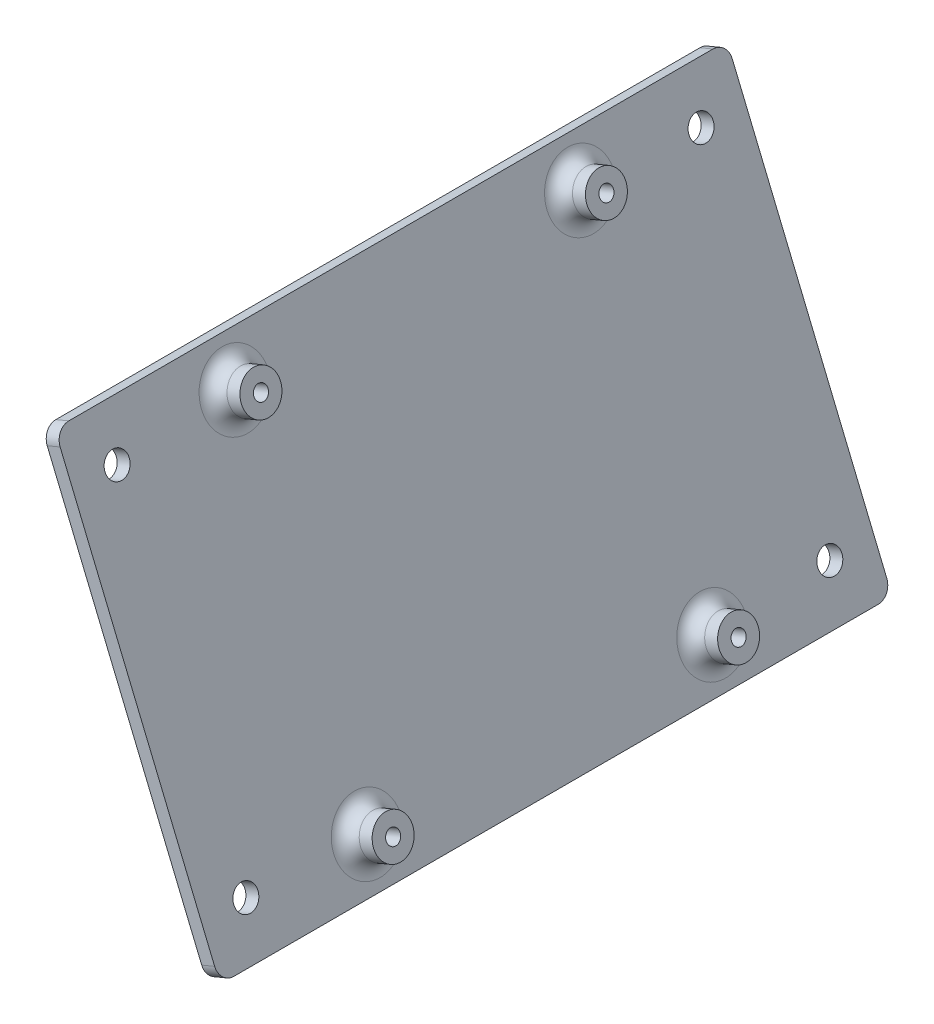
SolidWorks part; units mm, degrees
ref_plane "Front Plane" through (0, 0, 0) normal (0, 0, 1) x (1, 0, 0)
ref_plane "Top Plane" through (0, 0, 0) normal (0, 1, 0) x (1, 0, 0)
ref_plane "Right Plane" through (0, 0, 0) normal (1, 0, 0) x (0, 0, -1)
sketch "Sketch1" plane through (-3845.7441, -1594.7426, 0) normal (0.9237, 0.383, 0) x (0, 0, -1)
  line L7 (73.6876, -117.6203) -> (73.6876, -317.6453) construction
  line L8 (73.6876, -293.4018) -> (-78.7124, -293.4018)
  line L9 (73.6876, -293.4018) -> (73.6876, -195.6118)
  line L10 (73.6876, -195.6118) -> (-78.7124, -195.6118)
  line L11 (-78.7124, -293.4018) -> (-78.7124, -195.6118)
  line L12 (-78.7124, -117.6203) -> (-78.7124, -317.6453) construction
  line L13 (40.1546, -287.0518) -> (-45.1794, -287.0518) construction
  line L15 (-45.1794, -201.9618) -> (40.1546, -201.9618) construction
  dimension "D1" = 6.35
  dimension "D2" = 6.35
extrude "Boss-Extrude1" add sketch "Sketch1" along normal blind 3.175
sketch "Sketch2" plane through (-3842.8112, -1593.5264, 0) normal (0.9237, 0.383, 0) x (0, 0, -1)
  circle A0 centre (36.7526, -283.6268) radius 4.445
  circle A1 centre (-41.5774, -283.6268) radius 4.445
  circle A2 centre (-41.5774, -205.3868) radius 4.445
  circle A3 centre (36.7526, -205.3868) radius 4.445
  dimension "D1" = 8.89
extrude "Boss-Extrude2" add sketch "Sketch2" along normal blind 6.35
fillet "Fillet1" radius 3.175 4 edges at (-3735.8709, -1851.4145, 41.5774) (-3765.8407, -1779.142, 41.5774) (-3765.8407, -1779.142, -36.7526) (-3735.8709, -1851.4145, -36.7526)
sketch "Sketch4" plane through (-3836.9455, -1591.0941, 0) normal (0.9237, 0.383, 0) x (0, 0, -1)
  circle A0 centre (36.7526, -205.3868) radius 1.6 construction
  circle A1 centre (-41.5774, -205.3868) radius 1.6 construction
  circle A2 centre (-41.5774, -283.6268) radius 1.6 construction
  circle A3 centre (36.7526, -283.6268) radius 1.6 construction
  circle A4 centre (36.7526, -205.3868) radius 1.6
  circle A5 centre (-41.5774, -205.3868) radius 1.6
  circle A6 centre (-41.5774, -283.6268) radius 1.6
  circle A7 centre (36.7526, -283.6268) radius 1.6
extrude "Cut-Extrude1" cut sketch "Sketch4" against normal through all
fillet "Fillet2" radius 3.175 4 edges at (-3769.3487, -1774.8266, -73.6876) (-3731.8904, -1865.158, -73.6876) (-3769.3487, -1774.8266, 78.7124) (-3731.8904, -1865.158, 78.7124)
sketch "Sketch5" plane through (-3842.8112, -1593.5264, 0) normal (0.9237, 0.383, 0) x (0, 0, -1)
  line L0 (61.5876, -117.6203) -> (61.5876, -317.6453) construction
  line L1 (65.7876, -317.6453) -> (65.7876, -117.6203) construction
  line L2 (61.5876, -117.6203) -> (61.5876, -317.6453)
  line L3 (65.7876, -317.6453) -> (65.7876, -117.6203)
  line L4 (-70.8124, -117.6203) -> (-70.8124, -317.6453) construction
  line L5 (-66.6124, -317.6453) -> (-66.6124, -117.6203) construction
  line L6 (-70.8124, -117.6203) -> (-70.8124, -317.6453)
  line L7 (-66.6124, -317.6453) -> (-66.6124, -117.6203)
  line L8 (-68.7124, -244.5068) -> (-78.7124, -244.5068) construction
  line L9 (63.6876, -206.4068) -> (-68.7124, -206.4068) construction
  line L10 (63.6876, -206.4068) -> (63.6876, -282.6068) construction
  line L11 (63.6876, -282.6068) -> (-68.7124, -282.6068) construction
  line L12 (-68.7124, -206.4068) -> (-68.7124, -282.6068) construction
  line L13 (-78.7124, -198.7868) -> (-78.7124, -290.2268) construction
  line L14 (-2.5124, -293.4018) -> (-2.5124, -282.6068) construction
  line L15 (-75.5374, -293.4018) -> (70.5126, -293.4018) construction
  line L16 (65.7876, -293.4018) -> (61.5876, -293.4018) construction
  circle A0 centre (63.6876, -282.6068) radius 2.75
  circle A1 centre (63.6876, -206.4068) radius 2.75
  circle A2 centre (-68.7124, -206.4068) radius 2.75
  circle A3 centre (-68.7124, -282.6068) radius 2.75
  point P22 (63.6876, -293.4018)
  dimension "D2" = 5.5
  dimension "D1" = 76.2
extrude "Cut-Extrude2" cut sketch "Sketch5" against normal through all contours L2 A0 L3 | L2 A0 | L3 A0 | L2 A1 L3 | L2 A1 | L3 A1 | L6 A2 | L6 A2 L7 | L7 A2 | L6 A3 L7 | L7 A3 | L6 A3
